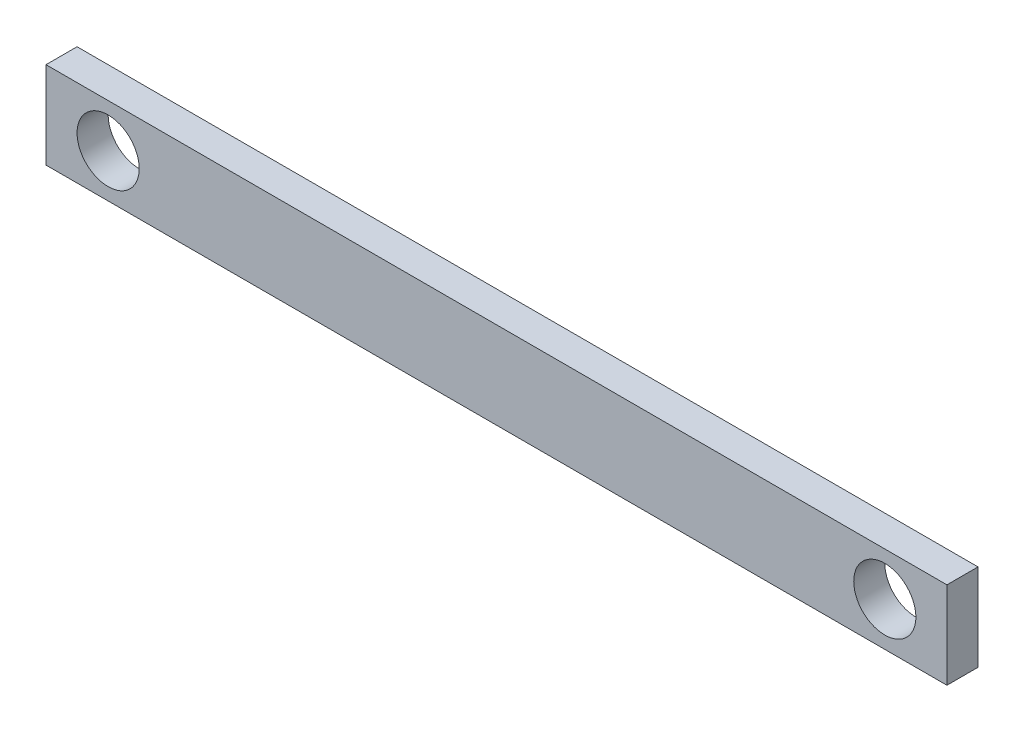
SolidWorks part; units mm, degrees
material "Plain Carbon Steel"
ref_plane "Front Plane" through (0, 0, 0) normal (0, 0, 1) x (1, 0, 0)
ref_plane "Top Plane" through (0, 0, 0) normal (0, 1, 0) x (1, 0, 0)
ref_plane "Right Plane" through (0, 0, 0) normal (1, 0, 0) x (0, 0, -1)
sketch "Sketch1" plane through (0, 0, 0) normal (0, 0, 1) x (1, 0, 0)
  line L0 (0, 0) -> (0, 140)
  line L1 (0, 140) -> (3930, 140)
  line L2 (3930, 140) -> (3930, 0)
  line L3 (3930, 0) -> (0, 0)
  dimension "D1" = 3930
  dimension "D2" = 140
extrude "Boss-Extrude1" add sketch "Sketch1" along normal blind 50
sketch "Sketch2" plane through (0, 0, 50) normal (0, 0, 1) x (1, 0, 0)
  line L0 (3930, 0) -> (3930, 140) construction
  line L1 (0, 140) -> (0, 0) construction
  circle A0 centre (3930, 70) radius 50
  circle A1 centre (0, 70) radius 50
  dimension "D1" = 100
  dimension "D2" = 100
extrude "Cut-Extrude1" cut sketch "Sketch2" against normal blind 50
sketch "Sketch3" plane through (0, 0, 0) normal (0, 0, -1) x (-1, 0, 0)
  line L0 (-3930, 140) -> (-4030, 140)
  line L1 (-4030, 140) -> (-4030, 0)
  line L2 (-4030, 0) -> (-3930, 0)
  line L3 (-3930, 0) -> (-3930, 140)
  line L4 (0, 140) -> (100, 140)
  line L5 (100, 140) -> (100, 0)
  line L6 (100, 0) -> (0, 0)
  line L7 (0, 0) -> (0, 140)
  dimension "D1" = 100
  dimension "D2" = 100
extrude "Boss-Extrude2" add sketch "Sketch3" against normal through all
sketch "Sketch4" plane through (0, 0, 0) normal (0, 0, -1) x (-1, 0, 0)
  line L0 (0, 120) -> (0, 20) construction
  line L1 (-3930, 20) -> (-3930, 120) construction
  circle A0 centre (0, 70) radius 50
  circle A1 centre (-3930, 70) radius 50
extrude "Cut-Extrude2" cut sketch "Sketch4" against normal through all
ref_plane "Plane1" through (0, 0, -10) normal (0, 0, -1) x (-1, 0, 0)
sketch "Sketch5" plane through (0, 0, -10) normal (0, 0, -1) x (-1, 0, 0)
  line L0 (-4030, 140) -> (-4030, 0)
  line L1 (-4030, 0) -> (-2580, 0)
  line L2 (100, 0) -> (-4030, 0) construction
  line L3 (-2580, 0) -> (-2580, 140)
  line L4 (-4030, 140) -> (100, 140) construction
  line L5 (-2580, 140) -> (-4030, 140)
  circle A0 centre (-3930, 70) radius 50
  circle A1 centre (-2680, 70) radius 50
  dimension "D1" = 100
  dimension "D3" = 100
  dimension "D2" = 100
  dimension "D4" = 1250
extrude "Boss-Extrude3" add sketch "Sketch5" along normal blind 50 separate body
sketch "Sketch6" plane through (0, 0, 50) normal (0, 0, 1) x (1, 0, 0)
  line L0 (-100, 140) -> (-100, 0)
  line L1 (-100, 0) -> (4030, 0)
  line L2 (4030, 0) -> (4030, 140)
  line L3 (4030, 140) -> (-100, 140)
extrude "Cut-Extrude3" cut sketch "Sketch6" against normal up to next (50 mm away)
